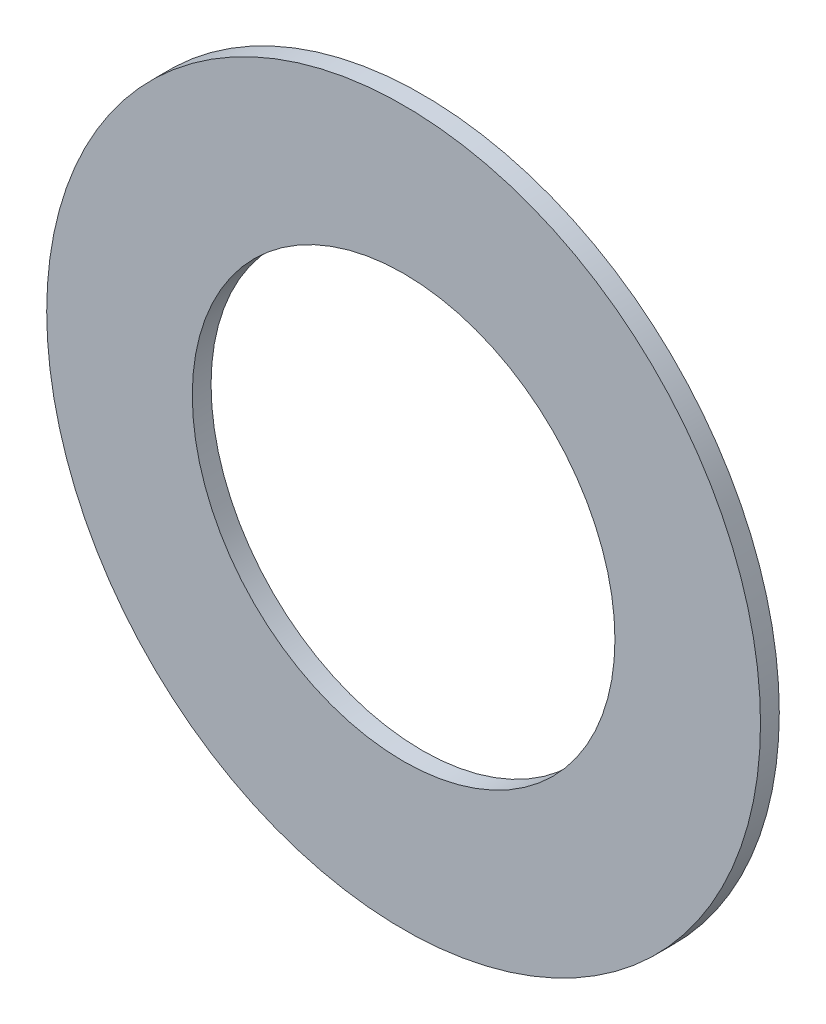
SolidWorks part; units mm, degrees
material "Rame"
ref_plane "Piano frontale" through (0, 0, 0) normal (0, 0, 1) x (1, 0, 0)
ref_plane "Piano superiore" through (0, 0, 0) normal (0, 1, 0) x (1, 0, 0)
ref_plane "Piano destro" through (0, 0, 0) normal (1, 0, 0) x (0, 0, -1)
sketch "Schizzo1" plane through (0, 0, 0) normal (0, 0, 1) x (1, 0, 0)
  circle A0 centre (0, 0) radius 19
  circle A1 centre (0, 0) radius 11.25
  dimension "D1" = 38
  dimension "D2" = 22.5
extrude "Estrusione-Estrusione1" add sketch "Schizzo1" along normal blind 1
